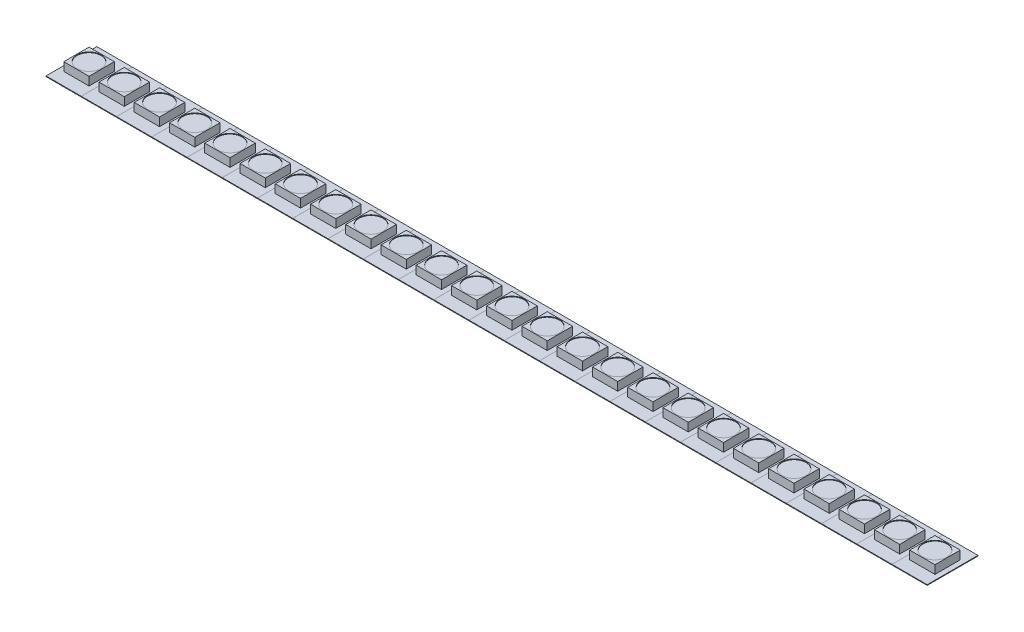
SolidWorks part; units mm, degrees
ref_plane "Front Plane" through (0, 0, 0) normal (0, 0, 1) x (1, 0, 0)
ref_plane "Top Plane" through (0, 0, 0) normal (0, 1, 0) x (1, 0, 0)
ref_plane "Right Plane" through (0, 0, 0) normal (1, 0, 0) x (0, 0, -1)
sketch "Sketch1" plane through (0, 0, 0) normal (0, 1, 0) x (1, 0, 0)
  line L0 (-3.4544, 4.9784) -> (3.4544, -4.9784) construction
  line L1 (-3.4544, 4.9784) -> (3.4544, 4.9784)
  line L2 (-3.4544, 4.9784) -> (-3.4544, -4.9784)
  line L3 (-3.4544, -4.9784) -> (3.4544, -4.9784)
  line L4 (3.4544, 4.9784) -> (3.4544, -4.9784)
  dimension "D1" = 9.9568
  dimension "D2" = 6.9088
extrude "Boss-Extrude1" add sketch "Sketch1" along normal blind 0.127
sketch "Sketch3" plane through (0, 0.127, 0) normal (0, 1, 0) x (1, 0, 0)
  line L0 (-3.4544, 4.9784) -> (3.4544, -4.9784) construction
  line L1 (-2.4765, 2.4765) -> (2.4765, -2.4765) construction
  line L2 (-2.4765, 2.4765) -> (2.4765, 2.4765)
  line L3 (-2.4765, 2.4765) -> (-2.4765, -2.4765)
  line L4 (-2.4765, -2.4765) -> (2.4765, -2.4765)
  line L5 (2.4765, 2.4765) -> (2.4765, -2.4765)
  dimension "D1" = 4.953
extrude "Boss-Extrude3" add sketch "Sketch3" along normal blind 1.651
sketch "Sketch5" plane through (0, 1.778, 0) normal (0, 1, 0) x (1, 0, 0)
  circle A0 centre (0, 0) radius 2.3483
extrude "Cut-Extrude1" cut sketch "Sketch5" against normal blind 0.127
pattern_linear "LPattern1" count 25 spacing 6.9088 along (1, 0, 0) of "Boss-Extrude3", "Cut-Extrude1", "Boss-Extrude1"
